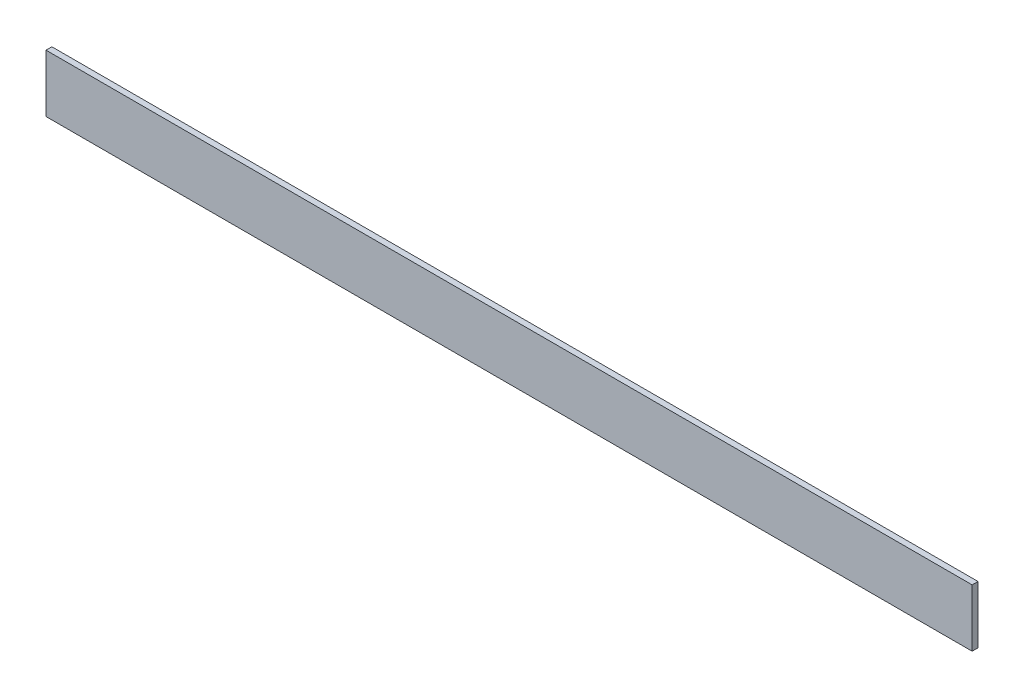
SolidWorks part; units mm, degrees
ref_plane "前视基准面" through (0, 0, 0) normal (0, 0, 1) x (1, 0, 0)
ref_plane "上视基准面" through (0, 0, 0) normal (0, 1, 0) x (1, 0, 0)
ref_plane "右视基准面" through (0, 0, 0) normal (1, 0, 0) x (0, 0, -1)
other "Configuration Table"
sketch "草图1" plane through (0, 0, 0) normal (0, 0, 1) x (1, 0, 0)
  line L1 (-236.665, 14.69) -> (236.665, 14.69)
  line L2 (-236.665, 14.69) -> (-236.665, -14.69)
  line L3 (-236.665, -14.69) -> (236.665, -14.69)
  line L4 (236.665, 14.69) -> (236.665, -14.69)
  line L5 (-236.665, 14.69) -> (236.665, -14.69) construction
  line L6 (-236.665, -14.69) -> (236.665, 14.69) construction
  point P0 (0, 0)
  dimension "D1" = 473.33
  dimension "D2" = 29.38
extrude "凸台-拉伸1" add sketch "草图1" along normal blind 3
